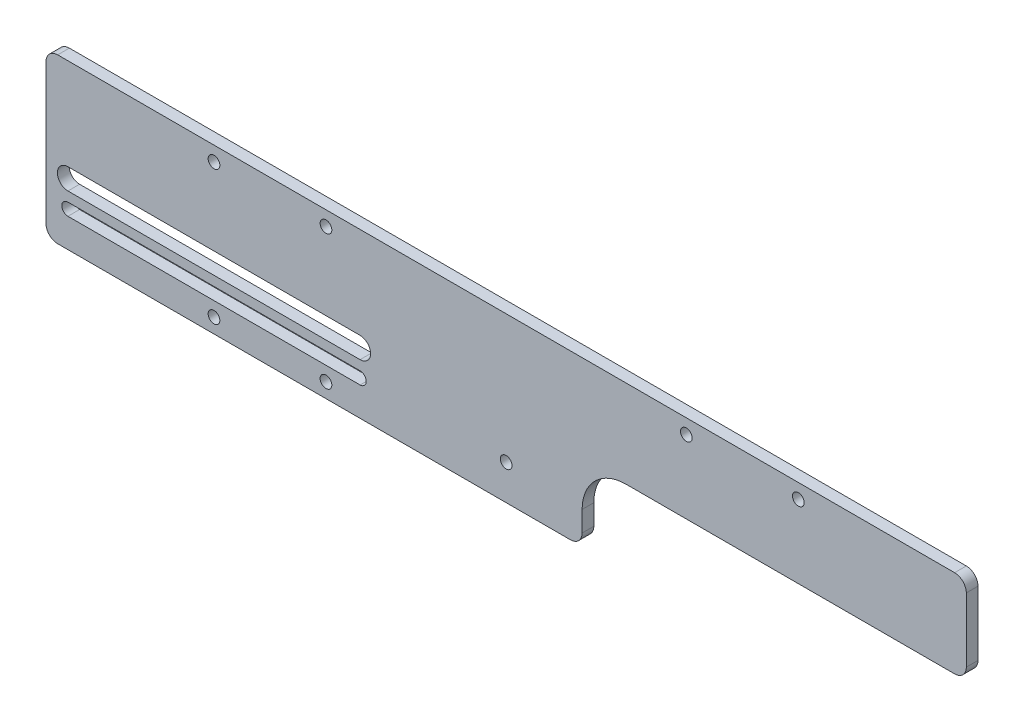
SolidWorks part; units mm, degrees
ref_plane "前视基准面" through (0, 0, 0) normal (0, 0, 1) x (1, 0, 0)
ref_plane "上视基准面" through (0, 0, 0) normal (0, 1, 0) x (1, 0, 0)
ref_plane "右视基准面" through (0, 0, 0) normal (1, 0, 0) x (0, 0, -1)
sketch "草图1" plane through (0, 0, 0) normal (0, 0, 1) x (1, 0, 0)
  line L0 (-150, -16) -> (-50, -16) construction
  line L1 (153.5, -28) -> (-153.5, -28)
  line L2 (157.5, -24) -> (157.5, 24)
  line L3 (153.5, 28) -> (-153.5, 28)
  line L4 (-157.5, -24) -> (-157.5, 24)
  line L5 (157.5, -28) -> (-157.5, 28) construction
  line L6 (157.5, 28) -> (-157.5, -28) construction
  line L7 (-150, -13.9) -> (-50, -13.9)
  line L8 (-150, -18.1) -> (-50, -18.1)
  line L9 (0, 28) -> (0, -28) construction
  arc A0 (157.5, -24) -> (153.5, -28) centre (153.5, -24) cw
  arc A1 (157.5, 24) -> (153.5, 28) centre (153.5, 24) ccw
  arc A2 (-157.5, -24) -> (-153.5, -28) centre (-153.5, -24) ccw
  arc A3 (-157.5, 24) -> (-153.5, 28) centre (-153.5, 24) cw
  arc A4 (-150, -13.9) -> (-150, -18.1) centre (-150, -16) ccw
  arc A5 (-50, -18.1) -> (-50, -13.9) centre (-50, -16) ccw
  circle A7 centre (-100, 23) radius 2
  circle A8 centre (-61.67, 23) radius 2
  circle A9 centre (-100, -23) radius 2
  circle A11 centre (-61.67, -23) radius 2
  circle A12 centre (100, -23) radius 2
  circle A13 centre (61.67, -23) radius 2
  circle A14 centre (61.67, 23) radius 2
  circle A15 centre (100, 23) radius 2
  point P0 (0, 0)
  point P20 (-100, -16)
  dimension "D3" = 4
  dimension "D5" = 7.5
  dimension "D6" = 2.1
  dimension "D7" = 46
  dimension "D8" = 5
  dimension "D9" = 12
  dimension "D10" = 4
  dimension "D11" = 4
  dimension "D12" = 4
  dimension "D13" = 4
  dimension "D14" = 38.33
  dimension "D15" = 38.33
  dimension "D16" = 46
  dimension "D17" = 5
  dimension "D18" = 5
  dimension "D19" = 100
  dimension "D20" = 12
  dimension "D1" = 315
  dimension "D2" = 56
  dimension "D4" = 100
extrude "凸台-拉伸1" add sketch "草图1" along normal blind 4
sketch "草图2" plane through (0, 0, 4) normal (0, 0, 1) x (1, 0, 0)
  line L0 (0, -24) -> (0, -12)
  line L1 (-153.5, -28) -> (153.5, -28) construction
  line L2 (153.5, 28) -> (-153.5, 28) construction
  line L3 (157.5, 2) -> (157.5, -28)
  line L4 (108, -2) -> (10, -2)
  line L5 (112, 28) -> (153.5, 28)
  line L6 (157.5, 24) -> (157.5, 2)
  line L7 (0, -28) -> (157.5, -28)
  line L8 (108, 28) -> (0, 28)
  line L9 (-4, -28) -> (-34.2058, -28)
  line L10 (112, 28) -> (108, 28)
  line L11 (0, -28) -> (-4, -28)
  line L12 (-4, -28) -> (0, -28)
  line L13 (108, -2) -> (153.5, -2)
  line L15 (108, 28) -> (153.5, 28)
  line L16 (157.5, -2) -> (157.5, 24)
  line L17 (0, -28) -> (-4, -28)
  line L18 (153.5, -2) -> (146.4628, -2)
  line L19 (146.4628, -2) -> (153.5, -2)
  arc A0 (-4, -28) -> (0, -24) centre (-4, -24) ccw
  arc A1 (0, -12) -> (10, -2) centre (10, -12) cw
  arc A2 (153.5, -2) -> (157.5, 2) centre (153.5, 2) ccw
  arc A3 (157.5, 24) -> (153.5, 28) centre (153.5, 24) ccw
  point P22 (112, 16)
  dimension "D3" = 4
  dimension "D2" = 10
  dimension "D4" = 4
  dimension "D1" = 30
extrude "切除-拉伸1" cut sketch "草图2" against normal blind 4
sketch "草图3" plane through (0, 0, 4) normal (0, 0, 1) x (1, 0, 0)
  line L0 (153.5, 28) -> (-153.5, 28) construction
  line L1 (-4, -28) -> (22, -28)
  line L2 (-4, -28) -> (-4, 28)
  line L3 (-4, 28) -> (26, 28)
  line L4 (26, -24) -> (26, 24)
  line L5 (30, 28) -> (43.0464, 28)
  line L6 (30, 28) -> (26, 28)
  arc A0 (30, 28) -> (26, 24) centre (30, 24) ccw
  arc A1 (26, -24) -> (22, -28) centre (22, -24) cw
  line M17 (153.5, 28) -> (-153.5, 28)
  arc M22 (-4, -28) -> (0, -24) centre (-4, -24) ccw
  line M23 (0, -24) -> (0, -12)
  arc M24 (0, -12) -> (10, -2) centre (10, -12) cw
  line M25 (10, -2) -> (153.5, -2)
  dimension "D2" = 4
  dimension "D1" = 30
extrude "凸台-拉伸2" add sketch "草图3" against normal blind 4 contours A0 L2 L4 M17 M22 M23 M24 M25 | A1 L4 L1 M25 M24 M23 M22
sketch "草图17" plane through (0, 0, 4) normal (0, 0, 1) x (1, 0, 0)
  line L0 (26, -8.7425) -> (26, -17)
  line L1 (26, -24) -> (26, -2) construction
  line L2 (41, -2) -> (54.4512, -2)
  line L3 (26, -2) -> (153.5, -2) construction
  line L4 (41, -2) -> (26, -2)
  line L5 (26, -2) -> (26, -17)
  arc A0 (41, -2) -> (26, -17) centre (41, -17) ccw
  point P10 (26, -2)
  line M8 (26, -24) -> (26, -2)
  line M9 (26, -2) -> (153.5, -2)
  dimension "D1" = 15
extrude "凸台-拉伸3" add sketch "草图17" against normal blind 4 contours A0 M9 M8
sketch "草图18" plane through (0, 0, 4) normal (0, 0, 1) x (1, 0, 0)
  line L0 (-153.5, -28) -> (22, -28) construction
  circle A0 centre (0, -16) radius 2
  arc A1 (-50, -18.1) -> (-50, -13.9) centre (-50, -16) ccw construction
  dimension "D1" = 12
  dimension "D2" = 50
extrude "切除-拉伸2" cut sketch "草图18" against normal through all
sketch "草图19" plane through (0, 0, 4) normal (0, 0, 1) x (1, 0, 0)
  line L0 (-50, -7) -> (-150, -7) construction
  line L1 (-50, -10.6) -> (-150, -10.6)
  line L2 (-50, -3.4) -> (-150, -3.4)
  arc A0 (-50, -10.6) -> (-50, -3.4) centre (-50, -7) ccw
  arc A1 (-150, -3.4) -> (-150, -10.6) centre (-150, -7) ccw
  arc A3 (-50, -18.1) -> (-50, -13.9) centre (-50, -16) ccw construction
  arc A4 (-150, -13.9) -> (-150, -18.1) centre (-150, -16) ccw construction
  point P2 (-100, -7)
  dimension "D1" = 3.6
  dimension "D2" = 9
  dimension "D3" = 9
  dimension "D4" = 100
extrude "切除-拉伸3" cut sketch "草图19" against normal through all
